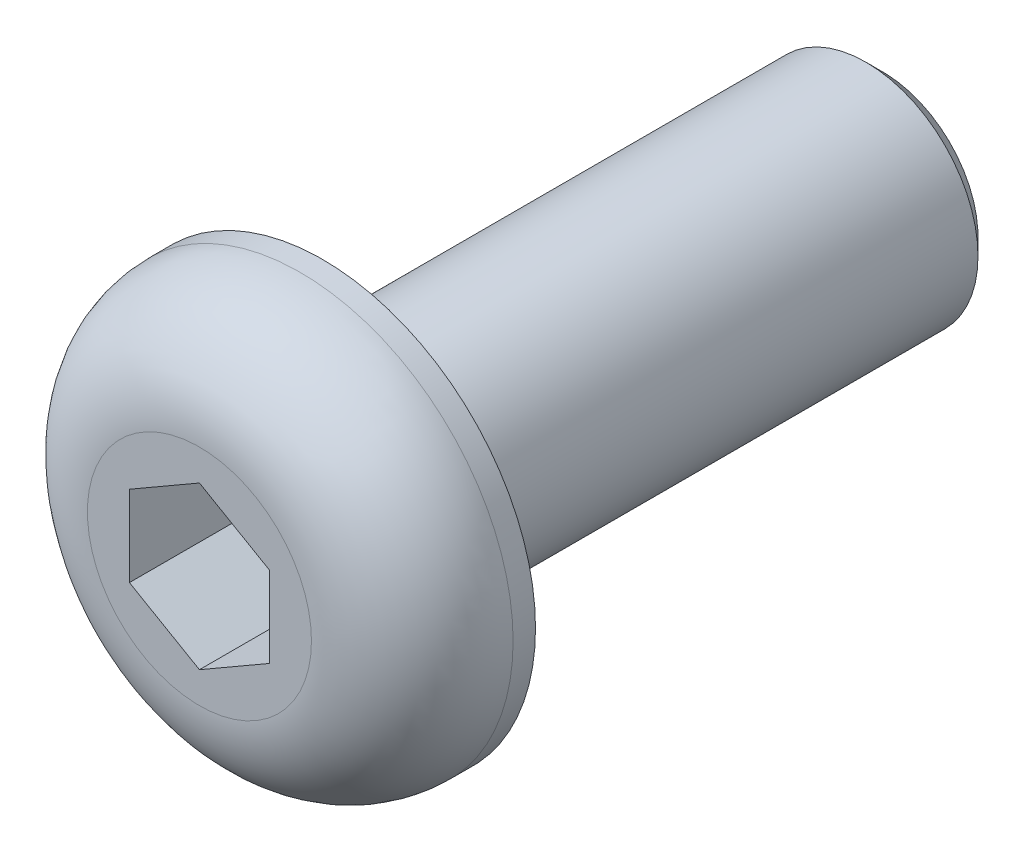
SolidWorks part; units mm, degrees
ref_plane "Front Plane" through (0, 0, 0) normal (0, 0, 1) x (1, 0, 0)
ref_plane "Top Plane" through (0, 0, 0) normal (0, 1, 0) x (1, 0, 0)
ref_plane "Right Plane" through (0, 0, 0) normal (1, 0, 0) x (0, 0, -1)
sketch "Sketch1" plane through (0, 0, 0) normal (0, 0, 1) x (1, 0, 0)
  circle A0 centre (0, 0) radius 3.8
  dimension "D1" = 7.6
extrude "Boss-Extrude1" add sketch "Sketch1" along normal blind 2.2
sketch "Sketch2" plane through (0, 0, 0) normal (0, 0, -1) x (-1, 0, 0)
  circle A0 centre (0, 0) radius 2
  dimension "D1" = 4
extrude "Boss-Extrude2" add sketch "Sketch2" along normal blind 10
chamfer "Chamfer1" distance 0.3 angle 45 1 edges at (-2, 0, -10)
sketch "Sketch3" plane through (0, 0, 2.2) normal (0, 0, 1) x (1, 0, 0)
  line L1 (0, 1.4434) -> (-1.25, 0.7217)
  line L2 (-1.25, 0.7217) -> (-1.25, -0.7217)
  line L3 (-1.25, -0.7217) -> (0, -1.4434)
  line L4 (0, -1.4434) -> (1.25, -0.7217)
  line L5 (1.25, -0.7217) -> (1.25, 0.7217)
  line L6 (1.25, 0.7217) -> (0, 1.4434)
  circle A0 centre (0, 0) radius 1.25 construction
  dimension "D1" = 2.5
extrude "Cut-Extrude1" cut sketch "Sketch3" against normal blind 2
fillet "Fillet1" radius 1.8 1 edges at (3.8, 0, 2.2)
